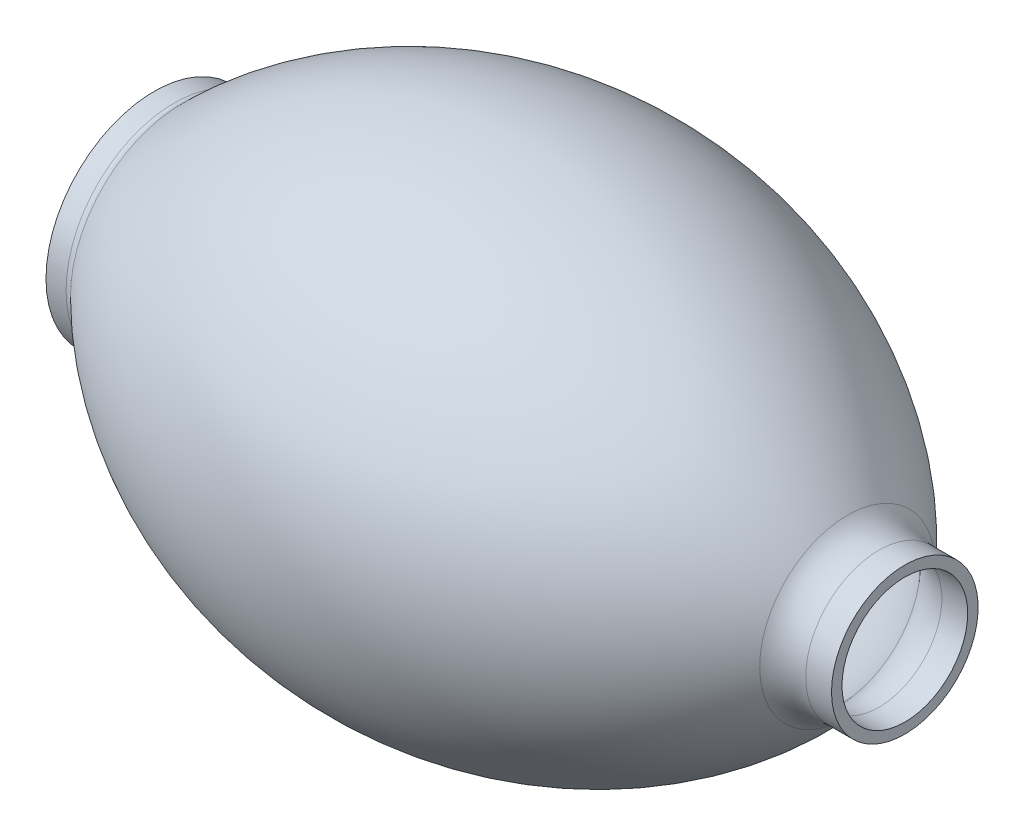
SolidWorks part; units mm, degrees
ref_plane "Front Plane" through (0, 0, 0) normal (0, 0, 1) x (1, 0, 0)
ref_plane "Top Plane" through (0, 0, 0) normal (0, 1, 0) x (1, 0, 0)
ref_plane "Right Plane" through (0, 0, 0) normal (1, 0, 0) x (0, 0, -1)
sketch "Croquis2" plane through (0, 0, 0) normal (0, 0, 1) x (1, 0, 0)
  line L0 (-97.5, 0) -> (97.5, 0) construction
  line L3 (0, 0) -> (0, 70) construction
  line L4 (103.1137, 21) -> (110.5, 21)
  line L5 (110.5, 21) -> (110.5, 0)
  line L7 (-97.5, 70) -> (84.5971, 70) construction
  line L8 (-98.7488, 31) -> (-104.5, 31)
  line L9 (-104.5, 31) -> (-104.5, 0)
  line L11 (-104.5, 0) -> (110.5, 0) construction
  line L12 (110.5, 0) -> (-104.5, 0)
  line L13 (-104.5, 0) -> (110.5, 0)
  arc A0 (94.0588, 25.1253) -> (-96.63, 31.8762) centre (-4.4376, -60.5334) ccw
  arc A1 (-98.7488, 31) -> (-96.63, 31.8762) centre (-98.7488, 34) ccw
  arc A2 (103.1137, 21) -> (94.0588, 25.1253) centre (103.1137, 33) cw
  point P16 (-97.5, 31)
  point P19 (97.5, 21)
  dimension "D8" = 3
  dimension "D9" = 12
  dimension "D1" = 31
  dimension "D2" = 195
  dimension "D3" = 21
  dimension "D4" = 97.5
  dimension "D5" = 70
  dimension "D6" = 13
  dimension "D7" = 7
revolve "Revolución1" add sketch "Croquis2" angle 360 about L13
shell "Vaciado1" thickness 3
